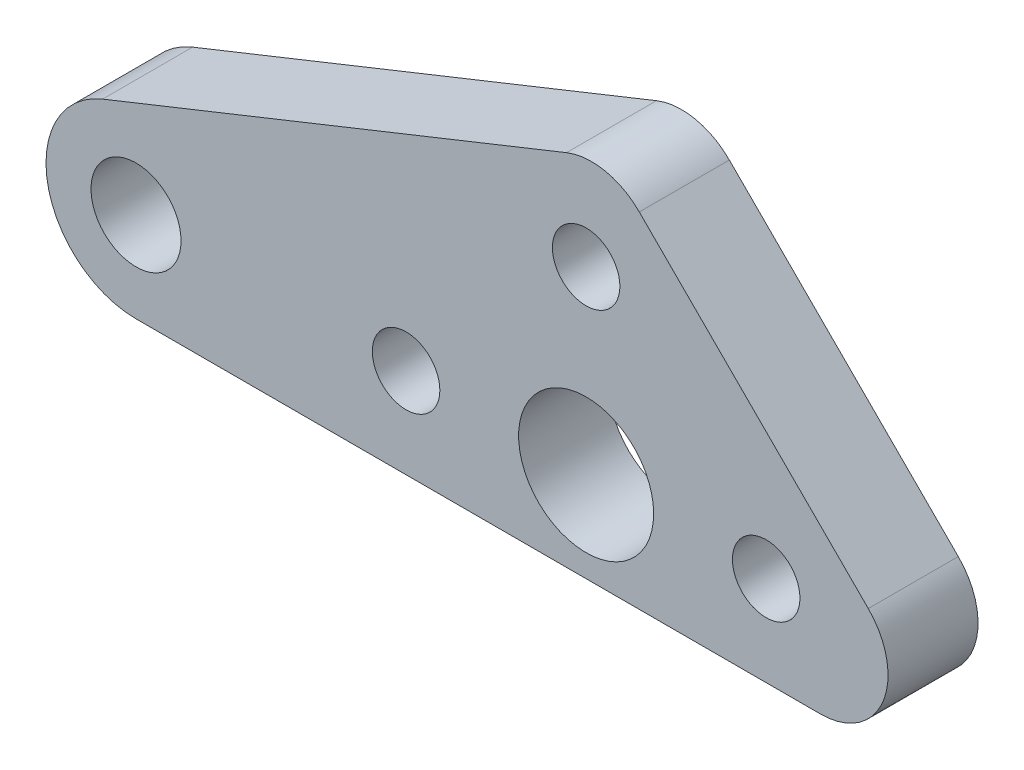
SolidWorks part; units mm, degrees
material "Thornel Mat VMA"
ref_plane "前视基准面" through (0, 0, 0) normal (0, 0, 1) x (1, 0, 0)
ref_plane "上视基准面" through (0, 0, 0) normal (0, 1, 0) x (1, 0, 0)
ref_plane "右视基准面" through (0, 0, 0) normal (1, 0, 0) x (0, 0, -1)
sketch "草图1" plane through (0, 0, 0) normal (0, 0, 1) x (1, 0, 0)
  line L0 (0, 0) -> (26.5183, 0) construction
  line L1 (0, 0) -> (0, 25.4802) construction
  line L2 (0, 8) -> (-20, 0) construction
  line L3 (-20, 0) -> (8, 0) construction
  line L4 (8, 0) -> (0, 8) construction
  line L5 (-0.8733, 11.9588) -> (-21.4856, 3.7139)
  line L6 (-20, -4) -> (10.4142, -4)
  line L7 (12.5355, 1.1213) -> (2.3622, 11.2947)
  line L8 (-40.7703, -4) -> (17.6569, -4) construction
  line L9 (17.6569, -4) -> (0.9634, 12.6935) construction
  line L10 (0.9634, 12.6935) -> (-40.7703, -4) construction
  circle A0 centre (0, 8) radius 1.5
  circle A1 centre (8, 0) radius 1.5
  circle A2 centre (-20, 0) radius 2
  arc A3 (10.4142, -4) -> (12.5355, 1.1213) centre (10.4142, -1) ccw
  arc A4 (-0.8733, 11.9588) -> (2.3622, 11.2947) centre (0.2408, 9.1734) cw
  arc A5 (-21.4856, 3.7139) -> (-20, -4) centre (-20, 0) ccw
  circle A6 centre (0, 0) radius 3
  circle A7 centre (-8, 0) radius 1.5
  dimension "D1" = 3
  dimension "D2" = 8
  dimension "D3" = 3
  dimension "D5" = 4
  dimension "D8" = 3
  dimension "D9" = 6
  dimension "D10" = 3
  dimension "D12" = 4
  dimension "D4" = 8
  dimension "D6" = 20
  dimension "D7" = 4
  dimension "D11" = 8
extrude "凸台-拉伸1" add sketch "草图1" along normal blind 4
sketch "草图2" plane through (0, 0, 4) normal (0, 0, 1) x (1, 0, 0)
  line L0 (-20, 0) -> (8, 0)
